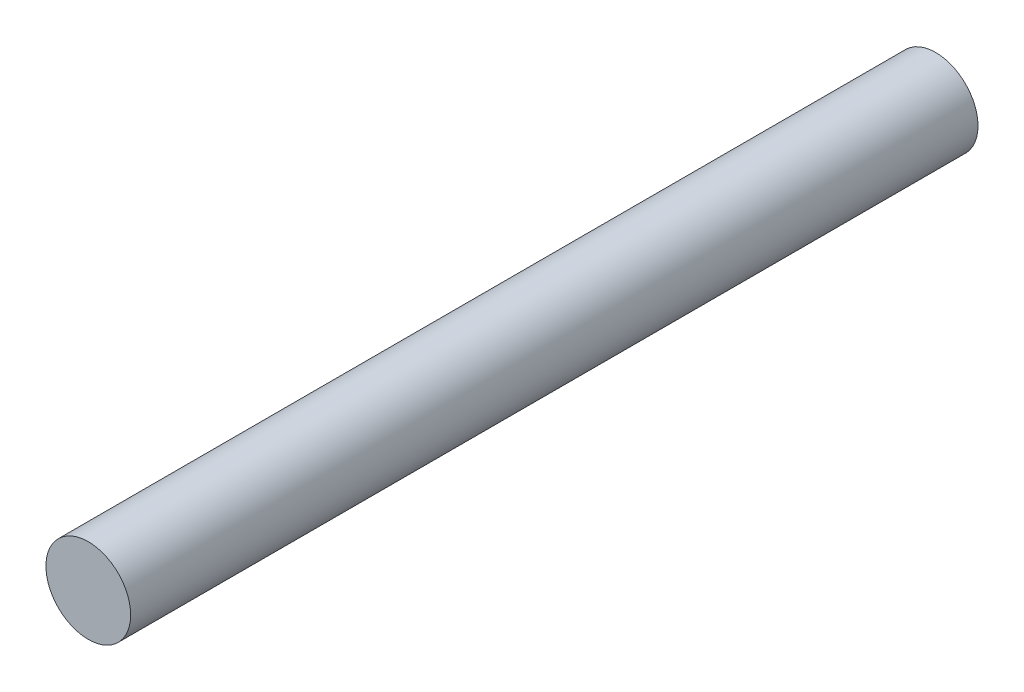
SolidWorks part; units mm, degrees
ref_plane "Front Plane" through (0, 0, 0) normal (0, 0, 1) x (1, 0, 0)
ref_plane "Top Plane" through (0, 0, 0) normal (0, 1, 0) x (1, 0, 0)
ref_plane "Right Plane" through (0, 0, 0) normal (1, 0, 0) x (0, 0, -1)
sketch "Sketch1" plane through (0, 0, 0) normal (0, 0, 1) x (1, 0, 0)
  circle A0 centre (0, 0) radius 6
  dimension "D1" = 12
extrude "Boss-Extrude1" add sketch "Sketch1" along normal blind 120
